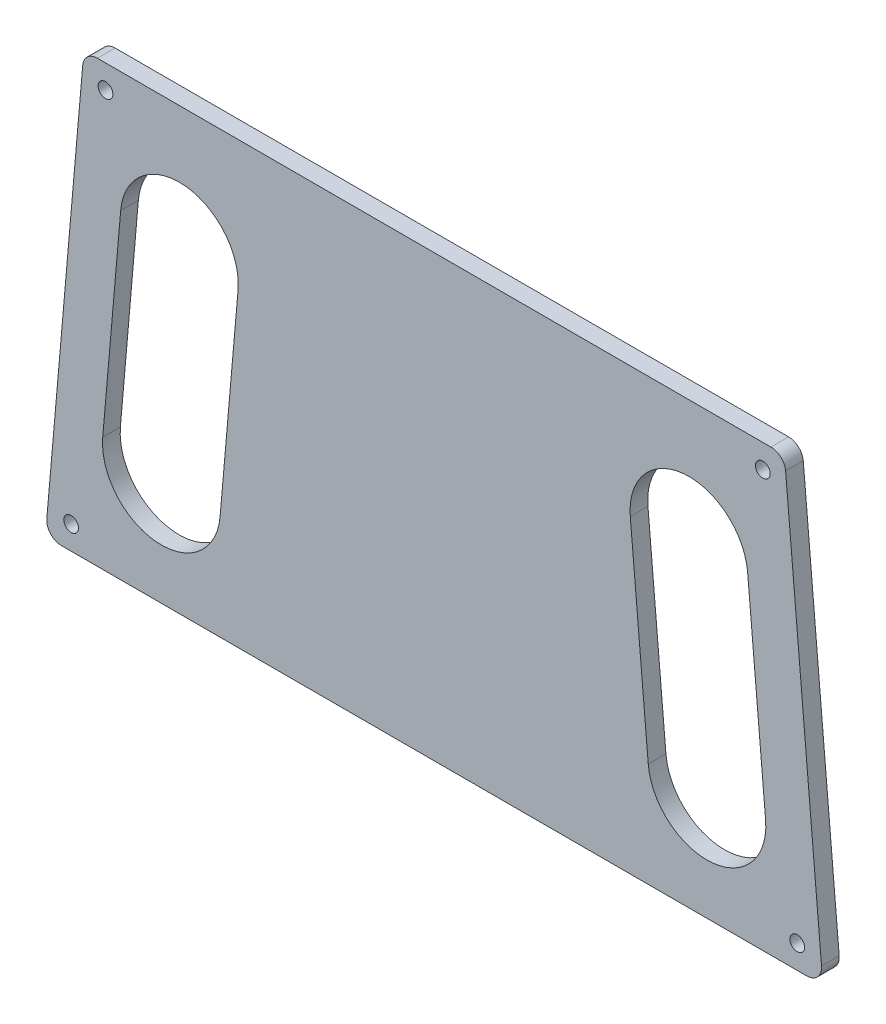
SolidWorks part; units mm, degrees
ref_plane "Front Plane" through (0, 0, 0) normal (0, 0, 1) x (1, 0, 0)
ref_plane "Top Plane" through (0, 0, 0) normal (0, 1, 0) x (1, 0, 0)
ref_plane "Right Plane" through (0, 0, 0) normal (1, 0, 0) x (0, 0, -1)
ref_plane "Plane1" through (0, 0, 11) normal (0, 0, 1) x (1, 0, 0)
sketch "Sketch1" plane through (0, 0, 11) normal (0, 0, 1) x (1, 0, 0)
  line L0 (53.2178, 54.3114) -> (56.2683, 19.4445)
  line L1 (36.3444, 17.7014) -> (33.2939, 52.5682)
  line L2 (-33.2939, 52.5682) -> (-36.3444, 17.7014)
  line L3 (-56.2683, 19.4445) -> (-53.2178, 54.3114)
  line L4 (57.1725, 74.7146) -> (-57.1725, 74.7146)
  line L5 (-59.663, 72.4325) -> (-65.7622, 2.7179)
  line L6 (-63.2717, 0) -> (63.2717, 0)
  line L7 (65.7622, 2.7179) -> (59.663, 72.4325)
  circle A0 centre (55.798, 70.7146) radius 1.25
  circle A1 centre (-61.6348, 4) radius 1.25
  circle A2 centre (-55.798, 70.7146) radius 1.25
  circle A3 centre (61.6348, 4) radius 1.25
  arc A4 (33.2939, 52.5682) -> (53.2178, 54.3114) centre (43.2559, 53.4398) cw
  arc A5 (56.2683, 19.4445) -> (36.3444, 17.7014) centre (46.3063, 18.573) cw
  arc A6 (-53.2178, 54.3114) -> (-33.2939, 52.5682) centre (-43.2559, 53.4398) cw
  arc A7 (-36.3444, 17.7014) -> (-56.2683, 19.4445) centre (-46.3063, 18.573) cw
  arc A8 (59.663, 72.4325) -> (57.1725, 74.7146) centre (57.1725, 72.2146) ccw
  arc A9 (-57.1725, 74.7146) -> (-59.663, 72.4325) centre (-57.1725, 72.2146) ccw
  arc A10 (-65.7622, 2.7179) -> (-63.2717, 0) centre (-63.2717, 2.5) ccw
  arc A11 (63.2717, 0) -> (65.7622, 2.7179) centre (63.2717, 2.5) ccw
extrude "Boss-Extrude1" add sketch "Sketch1" against normal blind 3
